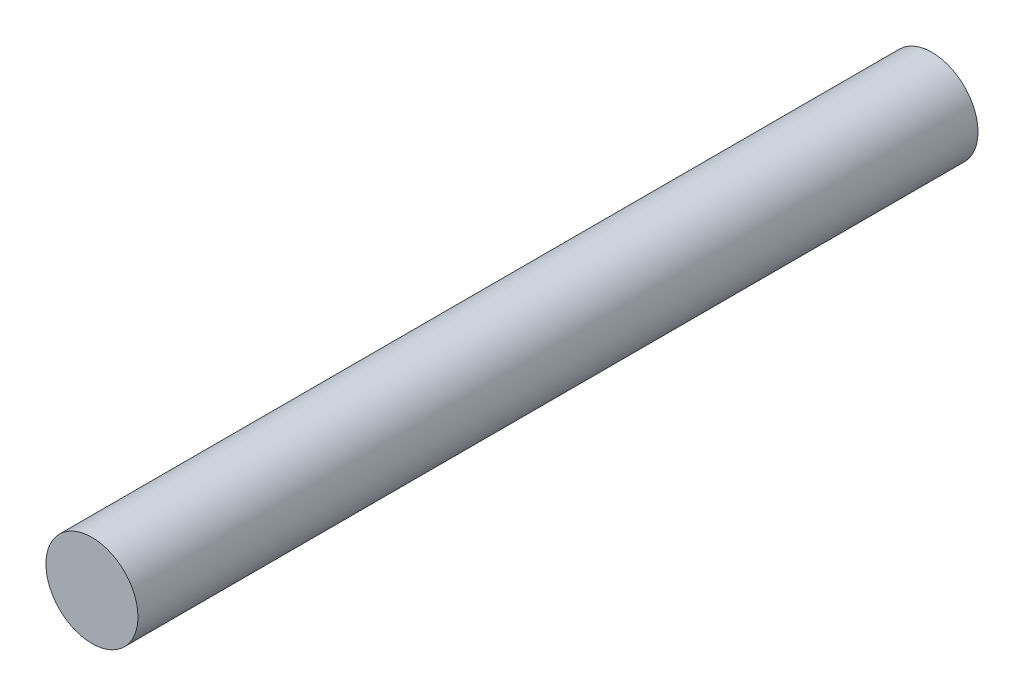
SolidWorks part; units mm, degrees
ref_plane "Front Plane" through (0, 0, 0) normal (0, 0, 1) x (1, 0, 0)
ref_plane "Top Plane" through (0, 0, 0) normal (0, 1, 0) x (1, 0, 0)
ref_plane "Right Plane" through (0, 0, 0) normal (1, 0, 0) x (0, 0, -1)
sketch "Sketch1" plane through (0, 0, 0) normal (0, 0, 1) x (1, 0, 0)
  circle A0 centre (0, 0) radius 4
  dimension "D1" = 8
extrude "Boss-Extrude1" add sketch "Sketch1" along normal blind 60
sketch "Sketch2" plane through (0, 0, 0) normal (0, 0, 1) x (1, 0, 0)
  circle A0 centre (0, 0) radius 4
  dimension "D1" = 8
extrude "Boss-Extrude2" add sketch "Sketch2" against normal blind 13
